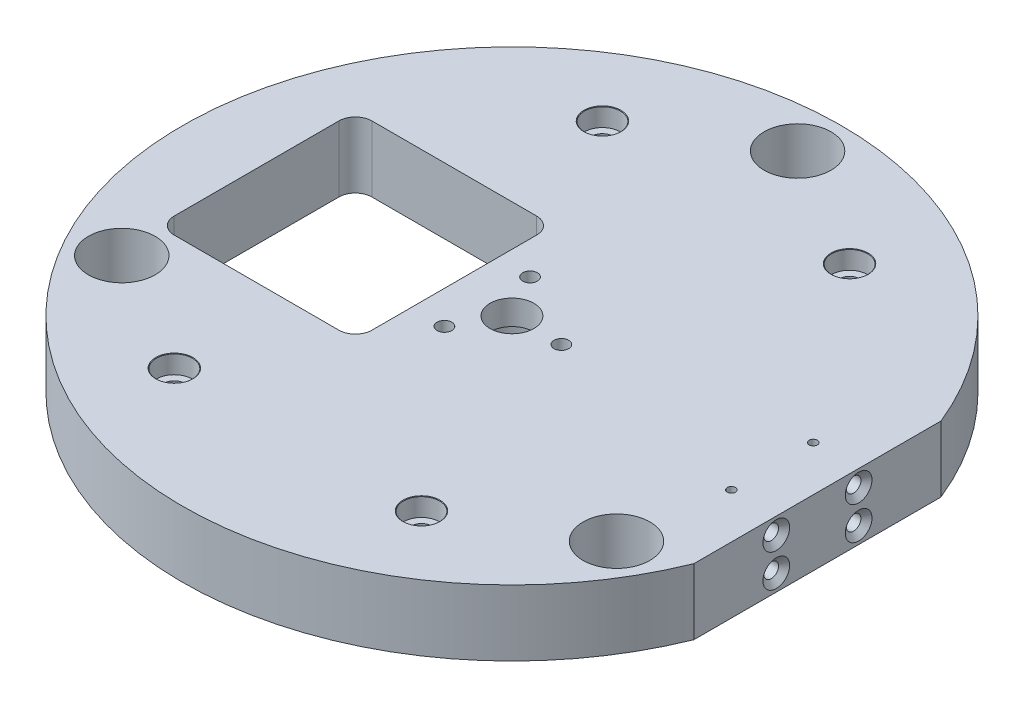
SolidWorks part; units mm, degrees
ref_plane "Front" through (0, 0, 0) normal (0, 0, 1) x (1, 0, 0)
ref_plane "Top" through (0, 0, 0) normal (0, 1, 0) x (1, 0, 0)
ref_plane "Right" through (0, 0, 0) normal (1, 0, 0) x (0, 0, -1)
sketch "Sketch1" plane through (0, 0, 0) normal (0, 1, 0) x (1, 0, 0)
  circle A0 centre (0, 0) radius 50.8
extrude "Boss-Extrude1" add sketch "Sketch1" along normal blind 10.16
sketch "Sketch2" plane through (0, 10.16, 0) normal (0, 1, 0) x (1, 0, 0)
  circle A0 centre (0, 44.0296) radius 5.15
  circle A1 centre (38.1308, -22.0148) radius 5.15
  circle A2 centre (-38.1308, -22.0148) radius 5.15
  point P8 (0, 0)
  point P9 (0, 0)
  dimension "D1" = 3
extrude "Cut-Extrude1" cut sketch "Sketch2" against normal through all
sketch "Sketch46" plane through (0, 10.16, 0) normal (0, 1, 0) x (1, 0, 0)
  line L0 (47.0929, 19.05) -> (47.0929, -19.05)
  circle A0 centre (0, 0) radius 50.8 construction
extrude "Cut-Extrude10" cut sketch "Sketch46" against normal through all and the other way through all
hole_wizard "CBORE for #4 Socket Head Cap Screw1" positions "Sketch35" profile "Sketch38" counterbore size "#4" standard "ANSI Inch"
sketch "Sketch35" plane through (0, 10.16, 0) normal (0, 1, 0) x (1, 0, 0)
  point P17 (-46.3725, 0) [skipped]
  point P19 (46.3725, 0) [skipped]
  point P21 (19.05, -32.9956)
  point P29 (-19.05, -32.9956)
  point P31 (-19.05, 32.9956)
  point P32 (19.05, 32.9956)
  point P38 (-38.1, 0) [skipped]
  point P42 (38.1, 0) [skipped]
  dimension "D2" = 6
sketch "Sketch38" plane through (19.05, 10.16, -32.9956) normal (1, 0, 0) x (0, 0, 1)
  line L0 (0, 0) -> (0, 10.16)
  line L1 (0, 10.16) -> (1.6319, 10.16)
  line L3 (1.6319, 10.16) -> (1.632, 2.8448)
  line L4 (2.7788, 2.8448) -> (1.632, 2.8448)
  line L5 (2.7788, 2.8448) -> (2.7788, 0.0661)
  line L6 (2.7788, 0.0661) -> (2.8575, 0)
  line L7 (2.8575, 0) -> (0, 0)
  line L8 (-2.7788, 0.0661) -> (-2.8575, 0) construction
  line L11 (0, -6.35) -> (0, 107.95) construction
  dimension "Thru Hole Dia." = 3.2639
  dimension "Thru Hole Depth" = 10.16
  dimension "C'Bore Dia." = 5.5575
  dimension "C'Bore Depth" = 2.8448
  dimension "Near C'Sink Dia." = 5.715
  dimension "Near C'Sink Angle" = 100
sketch "Sketch39" plane through (0, 10.16, 0) normal (0, 1, 0) x (1, 0, 0)
  line L0 (-39.37, 12.7) -> (-39.37, -12.7)
  line L1 (-36.83, -15.24) -> (-11.43, -15.24)
  line L2 (-8.89, -12.7) -> (-8.89, 12.7)
  line L3 (-11.43, 15.24) -> (-36.83, 15.24)
  arc A4 (-36.83, 15.24) -> (-39.37, 12.7) centre (-36.83, 12.7) ccw
  arc A5 (-8.89, 12.7) -> (-11.43, 15.24) centre (-11.43, 12.7) ccw
  arc A6 (-39.37, -12.7) -> (-36.83, -15.24) centre (-36.83, -12.7) ccw
  arc A7 (-8.89, -12.7) -> (-11.43, -15.24) centre (-11.43, -12.7) cw
extrude "Cut-Extrude9" cut sketch "Sketch39" against normal through all
hole_wizard "#4-40 Tapped Hole1" positions "Sketch40" profile "Sketch41" tap size "#4-40" standard "ANSI Inch" end condition through all
sketch "Sketch40" plane through (0, 10.16, 0) normal (0, 1, 0) x (1, 0, 0)
  point P0 (7.62, 0)
  point P6 (-3.81, -6.5991)
  point P7 (-3.81, 6.5991)
  dimension "D1" = 3
sketch "Sketch41" plane through (7.62, 10.16, 0) normal (1, 0, 0) x (0, 0, 1)
  line L0 (0, 0) -> (0, 10.16)
  line L1 (0, 10.16) -> (1.1303, 10.16)
  line L2 (1.1303, 10.16) -> (1.1303, 0)
  line L5 (1.1303, 0) -> (0, 0)
  line L11 (0, -6.35) -> (0, 107.95) construction
  dimension "Thru Tap Drill Dia." = 2.2606
  dimension "Thru Tap Drill Depth" = 10.16
cosmetic thread "Hole Thread9" parameters "D1"=10.16, "D2"=2.8448
cosmetic thread "Hole Thread10" parameters "D1"=10.16, "D2"=2.8448
cosmetic thread "Hole Thread11" parameters "D1"=10.16, "D2"=2.8448
hole_wizard "CBORE for 1/4 Socket Head Cap Screw1" positions "Sketch42" profile "Sketch44" counterbore size "1/4" standard "ANSI Inch" end condition through all
sketch "Sketch42" plane through (0, 0, 0) normal (0, -1, 0) x (-1, 0, 0)
  point P0 (0, 0)
sketch "Sketch44" plane through (0, 0, 0) normal (1, 0, 0) x (0, 0, -1)
  line L0 (0, 0) -> (0, 10.16)
  line L1 (0, 10.16) -> (3.3782, 10.16)
  line L3 (3.3782, 10.16) -> (3.3782, 6.35)
  line L4 (3.3782, 6.35) -> (5.5562, 6.35)
  line L5 (5.5562, 6.35) -> (5.5562, 0)
  line L7 (5.5562, 0) -> (0, 0)
  line L11 (0, -6.35) -> (0, 107.95) construction
  dimension "Thru Hole Dia." = 6.7564
  dimension "Thru Hole Depth" = 10.16
  dimension "C'Bore Dia." = 11.1125
  dimension "C'Bore Depth" = 6.35
hole_wizard "#97 (0.0059) Diameter Hole1" positions "Sketch52" profile "Sketch51" hole size "#97" standard "ANSI Inch" end condition through all
sketch "Sketch52" plane through (0, 10.16, 0) normal (0, 1, 0) x (1, 0, 0)
  point P0 (40.132, 6.3102)
  point P4 (40.132, 6.3102)
  point P6 (40.132, 6.3102)
  point P10 (40.132, -6.3102)
sketch "Sketch51" plane through (40.132, 10.16, -6.3102) normal (1, 0, 0) x (0, 0, 1)
  line L0 (0, 0) -> (0, 10.16)
  line L1 (0, 10.16) -> (0.635, 10.16)
  line L2 (0.635, 10.16) -> (0.635, 0)
  line L5 (0.635, 0) -> (0, 0)
  line L11 (0, -6.35) -> (0, 107.95) construction
  dimension "Thru Hole Dia." = 1.27
  dimension "Thru Hole Depth" = 10.16
hole_wizard "#4-40 Tapped Hole2" positions "Sketch53" profile "Sketch54" tap size "#4-40" standard "ANSI Inch"
sketch "Sketch53" plane through (47.0929, 0, 0) normal (1, 0, 0) x (0, 0, -1)
  point P0 (-6.35, 7.62)
  point P2 (-6.35, 2.54)
  point P4 (6.35, 7.62)
  point P6 (6.35, 2.54)
sketch "Sketch54" plane through (47.0929, 7.62, 6.35) normal (0, 1, 0) x (0, 0, -1)
  line L0 (0, 0) -> (0, 8.2738)
  line L1 (0, 8.2738) -> (1.1303, 7.5946)
  line L2 (1.1303, 7.5946) -> (1.1303, 0.7779)
  line L3 (1.1303, 0.7779) -> (2.0574, 0)
  line L5 (2.0574, 0) -> (0, 0)
  line L6 (-1.1303, 0.7779) -> (-2.0574, 0) construction
  line L10 (0, 8.2738) -> (-1.1303, 7.5946) construction
  line L11 (0, -6.35) -> (0, 107.95) construction
  dimension "Tap Drill Dia." = 2.2606
  dimension "Tap Drill Depth" = 7.5946
  dimension "Near C'Sink Dia." = 4.1148
  dimension "Near C'Sink Angle" = 100
  dimension "Drill Angle" = 118
cosmetic thread "Hole Thread12" parameters "D1"=5.6896, "D2"=2.8448
cosmetic thread "Hole Thread13" parameters "D1"=5.6896, "D2"=2.8448
cosmetic thread "Hole Thread14" parameters "D1"=5.6896, "D2"=2.8448
cosmetic thread "Hole Thread15" parameters "D1"=5.6896, "D2"=2.8448
